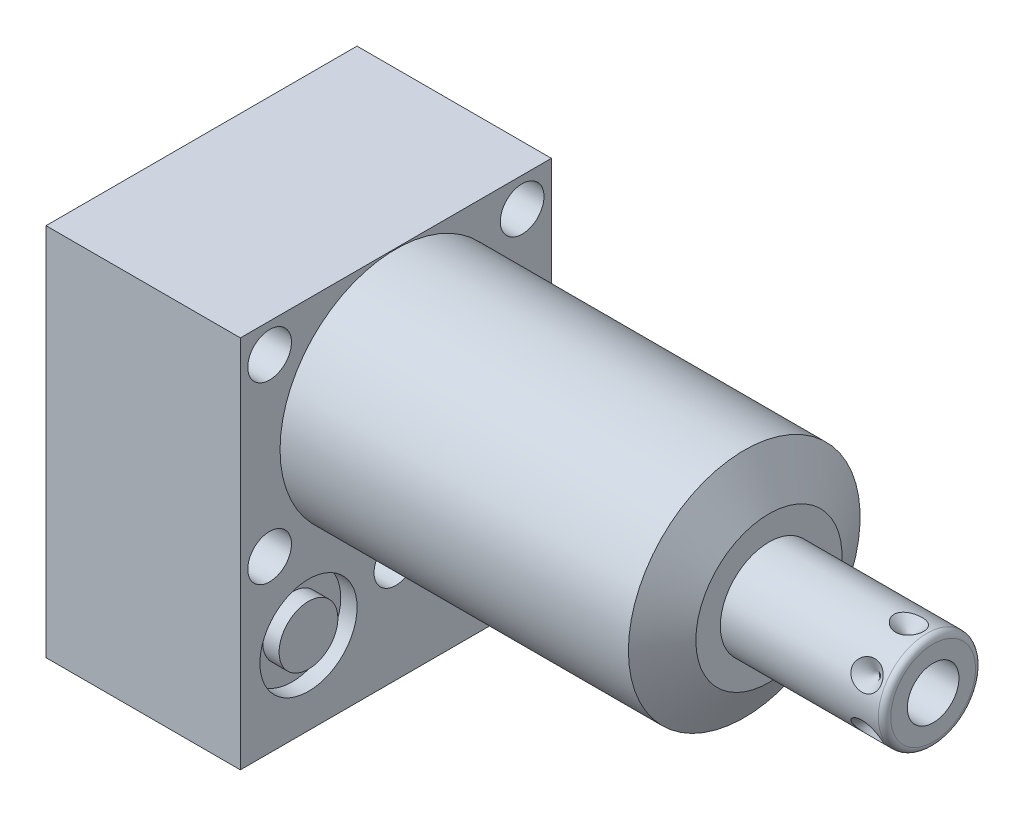
SolidWorks part; units mm, degrees
material "Alloy Steel"
ref_plane "Front Plane" through (0, 0, 0) normal (0, 0, 1) x (1, 0, 0)
ref_plane "Top Plane" through (0, 0, 0) normal (0, 1, 0) x (1, 0, 0)
ref_plane "Right Plane" through (0, 0, 0) normal (1, 0, 0) x (0, 0, -1)
ref_plane "Plane1" through (0, 0, 0) normal (1, 0, 0) x (0, 0, -1)
sketch "Sketch1" plane through (0, 0, 0) normal (1, 0, 0) x (0, 0, -1)
  line L0 (-25.4, 19.05) -> (-25.4, -42.0624)
  line L1 (-25.4, -42.0624) -> (25.4, -42.0624)
  line L2 (25.4, -42.0624) -> (25.4, 19.05)
  line L3 (25.4, 19.05) -> (-25.4, 19.05)
  line L4 (0, -47.0916) -> (0, 22.1996) construction
  dimension "D1" = 50.8
  dimension "D2" = 61.1124
  dimension "D3" = 19.05
extrude "Extrude1" add sketch "Sketch1" along normal blind 60.9346 and the other way blind 31.75
ref_plane "Plane2" through (0, 0, 0) normal (1, 0, 0) x (0, 0, -1)
sketch "Sketch2" plane through (0, 0, 0) normal (1, 0, 0) x (0, 0, -1)
  line L0 (-20.8153, 0) -> (20.8153, 0) construction
  line L6 (25.4, 19.05) -> (-25.4, 19.05)
  line L7 (-25.4, 19.05) -> (-25.4, -42.0624)
  line L8 (-25.4, -42.0624) -> (25.4, -42.0624)
  line L9 (25.4, -42.0624) -> (25.4, 19.05)
  line L10 (25.4, 19.05) -> (-25.4, 19.05)
  line L11 (-25.4, 19.05) -> (-25.4, -42.0624)
  line L12 (-25.4, -42.0624) -> (25.4, -42.0624)
  line L13 (25.4, -42.0624) -> (25.4, 19.05)
  circle A0 centre (0, 0) radius 18.923
  dimension "D1" = 37.846
  dimension "D2" = 0
extrude "Cut-Extrude1" cut sketch "Sketch2" along normal up to next
ref_plane "Plane3" through (0, 0, 0) normal (0, 0, 1) x (1, 0, 0)
sketch "Sketch3" plane through (0, 0, 0) normal (0, 0, 1) x (1, 0, 0)
  line L0 (56.9018, 18.923) -> (60.9346, 11.938)
  line L1 (56.7002, 0) -> (61.1362, 0) construction
  line L2 (60.9346, 18.923) -> (60.9346, 11.938)
  line L3 (60.9346, 18.923) -> (56.9018, 18.923)
  line L4 (60.9346, 18.923) -> (0, 18.923) construction
  line L5 (60.9346, -18.923) -> (60.9346, 18.923) construction
  dimension "D1" = 23.876
  dimension "D2" = 30
revolve "Cut-Revolve1" cut sketch "Sketch3" angle 360 about L1
ref_plane "Plane4" through (-29.083, -28.575, 14.2748) normal (0, 0, 1) x (0, 1, 0)
sketch "S2D0002" plane through (-29.083, -28.575, 14.2748) normal (0, 0, 1) x (0, 1, 0)
  line L0 (0, 0) -> (4.5466, 0)
  line L1 (4.5466, 0) -> (4.1066, -2.0701)
  line L2 (4.1066, -2.0701) -> (3.4544, -2.7223)
  line L3 (3.4544, -2.7223) -> (3.4544, -13.97)
  line L4 (3.4544, -13.97) -> (0, -13.97)
  line L5 (0, -13.97) -> (0, 0)
  line L6 (0, -14.6685) -> (0, 0.6985) construction
  dimension "D1" = 13.97
revolve "Cut-Revolve2" cut sketch "S2D0002" angle 360 about L6
ref_plane "Plane5" through (-29.083, -28.575, -14.2748) normal (0, 0, 1) x (0, 1, 0)
sketch "Sketch5" plane through (-29.083, -28.575, -14.2748) normal (0, 0, 1) x (0, 1, 0)
  line L0 (0, 0) -> (4.5466, 0)
  line L1 (4.5466, 0) -> (4.1066, -2.0701)
  line L2 (4.1066, -2.0701) -> (3.4544, -2.7223)
  line L3 (3.4544, -2.7223) -> (3.4544, -13.97)
  line L4 (3.4544, -13.97) -> (0, -13.97)
  line L5 (0, -13.97) -> (0, 0)
  line L6 (0, -14.6685) -> (0, 0.6985) construction
  dimension "D1" = 13.97
revolve "Cut-Revolve3" cut sketch "Sketch5" angle 360 about L6
ref_plane "Plane6" through (-2.667, -28.575, 14.2748) normal (0, 0, 1) x (0, -1, 0)
sketch "Sketch6" plane through (-2.667, -28.575, 14.2748) normal (0, 0, 1) x (0, -1, 0)
  line L0 (0, 0) -> (4.5466, 0)
  line L1 (4.5466, 0) -> (4.1066, -2.0701)
  line L2 (4.1066, -2.0701) -> (3.4544, -2.7223)
  line L3 (3.4544, -2.7223) -> (3.4544, -12.192)
  line L4 (3.4544, -12.192) -> (0, -12.192)
  line L5 (0, -12.192) -> (0, 0)
  line L6 (0, -12.8016) -> (0, 0.6096) construction
  dimension "D1" = 12.192
revolve "Cut-Revolve4" cut sketch "Sketch6" angle 360 about L6
ref_plane "Plane7" through (-2.667, -28.575, -14.2748) normal (0, 0, 1) x (0, -1, 0)
sketch "Sketch7" plane through (-2.667, -28.575, -14.2748) normal (0, 0, 1) x (0, -1, 0)
  line L0 (0, 0) -> (4.5466, 0)
  line L1 (4.5466, 0) -> (4.1066, -2.0701)
  line L2 (4.1066, -2.0701) -> (3.4544, -2.7223)
  line L3 (3.4544, -2.7223) -> (3.4544, -12.192)
  line L4 (3.4544, -12.192) -> (0, -12.192)
  line L5 (0, -12.192) -> (0, 0)
  line L6 (0, -12.8016) -> (0, 0.6096) construction
  dimension "D1" = 12.192
revolve "Cut-Revolve5" cut sketch "Sketch7" angle 360 about L6
ref_plane "Plane8" through (-15.875, -43.688, 14.2748) normal (0, 0, 1) x (-1, 0, 0)
sketch "Sketch18" plane through (-31.75, 0, 0) normal (-1, 0, 0) x (0, 0, 1)
  circle A0 centre (-14.2748, -28.575) radius 7.9375
  circle A1 centre (14.2748, -28.575) radius 7.9375
  dimension "D1" = 15.875
  dimension "D2" = 15.875
extrude "Cut-Extrude2" cut sketch "Sketch18" against normal blind 2.667
sketch "Sketch19" plane through (0, 0, 0) normal (1, 0, 0) x (0, 0, -1)
  circle A0 centre (-14.2748, -28.575) radius 7.9375
  circle A1 centre (14.2748, -28.575) radius 7.9375
  dimension "D1" = 15.875
  dimension "D2" = 15.875
extrude "Cut-Extrude3" cut sketch "Sketch19" against normal blind 2.667
sketch "Sketch8" plane through (-15.875, -43.688, 14.2748) normal (0, 0, 1) x (-1, 0, 0)
  line L0 (0, -1.8796) -> (6.1849, -1.8796)
  line L1 (6.1849, -1.8796) -> (5.6423, -4.4323)
  line L2 (5.6423, -4.4323) -> (4.9784, -5.0962)
  line L3 (4.9784, -5.0962) -> (4.9784, -20.9296)
  line L4 (4.9784, -20.9296) -> (0, -20.9296)
  line L5 (0, -20.9296) -> (0, -1.8796)
  line L6 (0, -26.67) -> (0, 1.27) construction
  line L7 (15.875, -1.6256) -> (-15.875, -1.6256) construction
  dimension "D1" = 19.05
  dimension "D2" = 0.254
revolve "Cut-Revolve6" cut sketch "Sketch8" angle 360 about L6
ref_plane "Plane9" through (-15.875, -43.688, -14.2748) normal (0, 0, 1) x (-1, 0, 0)
sketch "Sketch9" plane through (-15.875, -43.688, -14.2748) normal (0, 0, 1) x (-1, 0, 0)
  line L0 (0, -1.8796) -> (6.1849, -1.8796)
  line L1 (6.1849, -1.8796) -> (5.6423, -2.5527)
  line L2 (5.6423, -2.5527) -> (4.9784, -3.2166)
  line L3 (4.9784, -3.2166) -> (4.9784, -20.9296)
  line L4 (4.9784, -20.9296) -> (0, -20.9296)
  line L5 (0, -20.9296) -> (0, -1.8796)
  line L6 (0, -26.67) -> (0, 1.27) construction
  line L7 (15.875, -1.6256) -> (-15.875, -1.6256) construction
  dimension "D1" = 19.05
  dimension "D2" = 0.254
revolve "Cut-Revolve7" cut sketch "Sketch9" angle 360 about L6
ref_plane "Plane10" through (0, 0, 0) normal (0, 0, 1) x (1, 0, 0)
sketch "Sketch20" plane through (0, -42.0624, 0) normal (0, -1, 0) x (1, 0, 0)
  circle A0 centre (-15.875, 14.2748) radius 9.525
  circle A1 centre (-15.875, -14.2748) radius 9.525
  dimension "D1" = 19.05
extrude "Cut-Extrude4" cut sketch "Sketch20" against normal blind 0.254
sketch "Sketch10" plane through (0, 0, 0) normal (0, 0, 1) x (1, 0, 0)
  line L0 (60.9346, 0) -> (60.9346, 7.9375)
  line L1 (60.9346, 7.9375) -> (86.741, 7.9375)
  line L2 (87.757, 6.9215) -> (87.757, 0)
  line L3 (87.757, 0) -> (60.9346, 0)
  line L4 (59.5935, 0) -> (89.0981, 0) construction
  line L5 (60.9346, -11.938) -> (60.9346, 11.938) construction
  line L6 (-31.75, 19.05) -> (-31.75, -42.0624) construction
  arc A0 (87.757, 6.9215) -> (86.741, 7.9375) centre (86.741, 6.9215) ccw
  point P0 (60.9346, 0)
  dimension "D2" = 1.016
  dimension "D1" = 15.875
  dimension "D3" = 119.507
revolve "Revolve1" add sketch "Sketch10" angle 360 about L4
ref_plane "Plane11" through (87.757, -4.2164, 0) normal (0, 0, 1) x (0, -1, 0)
sketch "S2D0001" plane through (87.757, -4.2164, 0) normal (0, 0, 1) x (0, -1, 0)
  line L0 (0, 0) -> (0, -15.24)
  line L1 (0, -15.24) -> (-4.2164, -17.7735)
  line L2 (0, 0) -> (-4.2164, 0)
  line L3 (-4.2164, 0) -> (-4.2164, -17.7735)
  line L4 (-4.2164, -24.865) -> (-4.2164, 0.8887) construction
  line L5 (2.7051, 0) -> (-11.1379, 0) construction
  dimension "D1" = 8.4328
  dimension "D2" = 59
  dimension "D3" = 15.24
revolve "Cut-Revolve8" cut sketch "S2D0001" angle 360 about L4
ref_plane "Plane12" through (-31.75, -43.688, 0) normal (0, -1, 0) x (0, 0, -1)
sketch "Sketch12" plane through (-31.75, -41.8084, 0) normal (0, -1, 0) x (0, 0, -1)
  circle A0 centre (-14.2748, 15.875) radius 6.4389
  circle A1 centre (-14.2748, 15.875) radius 9.525 construction
  dimension "D1" = 12.8778
extrude "Extrude2" add sketch "Sketch12" along normal blind 1.651
sketch "Sketch13" plane through (0, 0, 0) normal (1, 0, 0) x (0, 0, -1)
  circle A0 centre (-14.2748, -28.575) radius 4.8006
  circle A1 centre (-14.2748, -28.575) radius 4.5466 construction
  dimension "D1" = 9.6012
ref_plane "Plane13" through (-31.75, 0, 0) normal (1, 0, 0) x (0, 0, -1)
extrude "Extrude3" add sketch "Sketch13" along normal up to surface (2.667 mm away)
ref_plane "Plane14" through (0, -28.575, -14.2748) normal (0, -1, 0) x (0, 0, -1)
sketch "Sketch14" plane through (0, -28.575, -14.2748) normal (0, -1, 0) x (0, 0, -1)
  line L0 (0, -2.8435) -> (0, 1.0401) construction
  line L1 (0, -2.667) -> (0, -4.7371) construction
  line L2 (7.9375, -2.667) -> (-7.9375, -2.667) construction
  circle A0 centre (6.1722, -0.9017) radius 1.7653
  dimension "D1" = 3.5306
  dimension "D2" = 12.3444
revolve "Revolve2" add sketch "Sketch14" angle 360 about L0
ref_plane "Plane15" through (0, -28.575, -14.2748) normal (0, -1, 0) x (0, 0, -1)
sketch "Sketch15" plane through (0, -28.575, -14.2748) normal (0, -1, 0) x (0, 0, -1)
  line L0 (0, -32.7901) -> (0, -28.9065) construction
  line L1 (0, -26.3607) -> (0, -19.4599) construction
  line L2 (-7.9375, -29.083) -> (7.9375, -29.083) construction
  circle A0 centre (6.1722, -30.8483) radius 1.7653
  dimension "D1" = 3.5306
  dimension "D2" = 12.3444
revolve "Revolve3" add sketch "Sketch15" angle 360 about L0
ref_plane "Plane16" through (83.7946, -7.9375, 0) normal (0, 0, 1) x (-1, 0, 0)
sketch "Sketch16" plane through (83.7946, -7.9375, 0) normal (0, 0, 1) x (-1, 0, 0)
  line L0 (0, 0) -> (2.413, 0)
  line L1 (2.413, 0) -> (0, -2.413)
  line L2 (0, 0) -> (0, -2.413)
  line L3 (0, -3.8054) -> (0, 0.1207) construction
  line L4 (22.86, 0) -> (-2.9464, 0) construction
  line L5 (-3.9624, -1.016) -> (-3.9624, -14.859) construction
  dimension "D1" = 3.9624
  dimension "D2" = 4.826
  dimension "D3" = 45
revolve "Cut-Revolve9" cut sketch "Sketch16" angle 360 about L3
pattern_circular "CirPattern1" count 6 over 360 about axis through (60.9356, 0, 0) along (-1, 0, 0) of "Cut-Revolve9"
hole_wizard "Hole1" positions "Sketch22" profile "Sketch21" legacy end condition up to next
sketch "Sketch22" plane through (0, 0, 0) normal (1, 0, 0) x (0, 0, -1)
  line L0 (0, 0) -> (-32.1908, 0) construction
  point P0 (-20.6248, 14.2748)
  point P1 (0, -25.0952)
  point P13 (-20.6248, -14.2748)
  point P14 (20.6248, 14.2748)
  point P15 (20.6248, -14.2748)
  dimension "D2" = 14.2748
  dimension "D3" = 25.0952
sketch "Sketch21" plane through (0, 14.2748, 20.6248) normal (0, 1, 0) x (0, 0, -1)
  line L0 (0, 0) -> (0, 31.75)
  line L1 (0, 31.75) -> (3.5687, 31.75)
  line L2 (3.5687, 31.75) -> (3.5687, 0)
  line L3 (3.5687, 0) -> (0, 0)
  line L4 (0, 110) -> (0, -10) construction
  dimension "Diameter" = 7.1374
  dimension "Depth" = 31.75
sketch "Sketch24" plane through (-29.083, 0, 0) normal (-1, 0, 0) x (0, 0, 1)
  circle A0 centre (14.2748, -28.575) radius 4.8006
  dimension "D1" = 9.6012
extrude "Extrude4" add sketch "Sketch24" along normal blind 2.667
